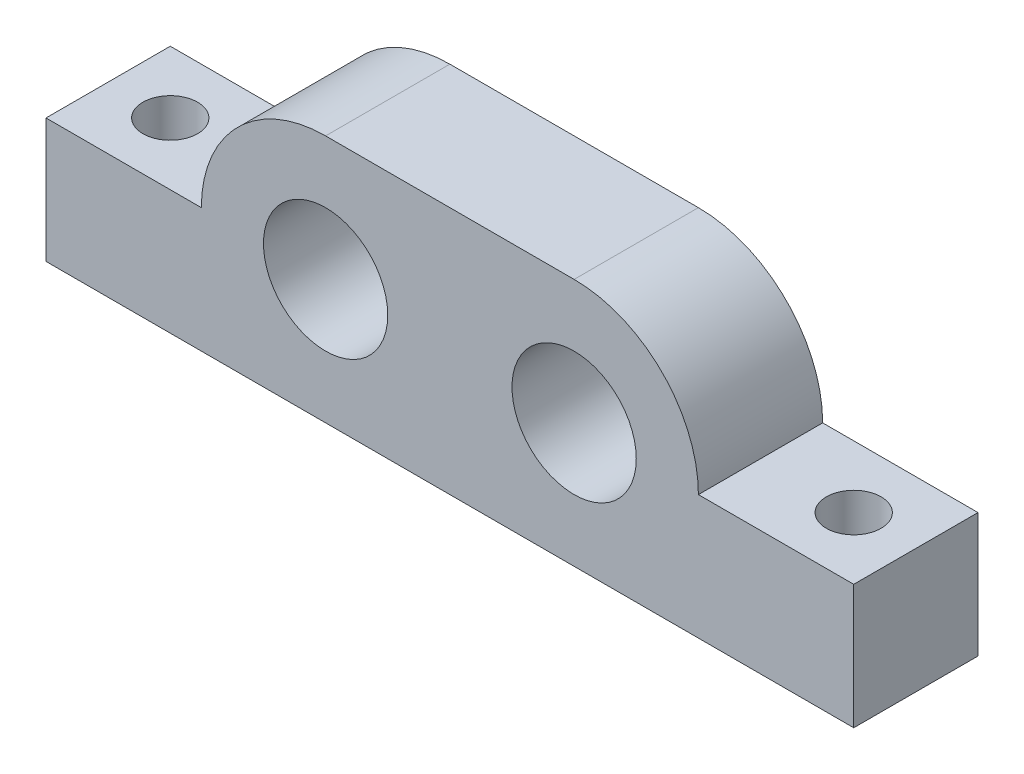
SolidWorks part; units mm, degrees
material "6061-T6 (SS)"
ref_plane "Front Plane" through (0, 0, 0) normal (0, 0, 1) x (1, 0, 0)
ref_plane "Top Plane" through (0, 0, 0) normal (0, 1, 0) x (1, 0, 0)
ref_plane "Right Plane" through (0, 0, 0) normal (1, 0, 0) x (0, 0, -1)
sketch "Sketch1" plane through (0, 0, 0) normal (0, 0, 1) x (1, 0, 0)
  line L0 (0, 0) -> (41.275, 0)
  line L1 (0, 0) -> (0, 6.35)
  line L2 (41.275, 0) -> (41.275, 6.35)
  line L3 (0, 6.35) -> (7.9375, 6.35)
  line L4 (41.275, 6.35) -> (33.3375, 6.35)
  line L6 (14.2875, 12.7) -> (26.9875, 12.7)
  arc A0 (7.9375, 6.35) -> (14.2875, 12.7) centre (14.2875, 6.35) cw
  arc A1 (33.3375, 6.35) -> (26.9875, 12.7) centre (26.9875, 6.35) ccw
  circle A2 centre (14.2875, 6.35) radius 3.175
  circle A3 centre (26.9875, 6.35) radius 3.175
  dimension "D2" = 6.35
  dimension "D3" = 6.35
  dimension "D6" = 6.35
  dimension "D1" = 41.275
  dimension "D4" = 6.35
  dimension "D5" = 7.9375
extrude "Boss-Extrude1" add sketch "Sketch1" along normal blind 6.35
sketch "Sketch2" plane through (0, 6.35, 0) normal (0, 1, 0) x (1, 0, 0)
  line L0 (7.9375, 0) -> (0, 0) construction
  line L1 (0, -6.35) -> (0, 0) construction
  line L2 (41.275, -6.35) -> (41.275, 0) construction
  circle A0 centre (38.1, -3.175) radius 1.397
  circle A1 centre (3.175, -3.175) radius 1.397
  dimension "D3" = 2.794
  dimension "D1" = 3.175
  dimension "D2" = 3.175
  dimension "D4" = 3.175
extrude "Cut-Extrude1" cut sketch "Sketch2" against normal up to next
